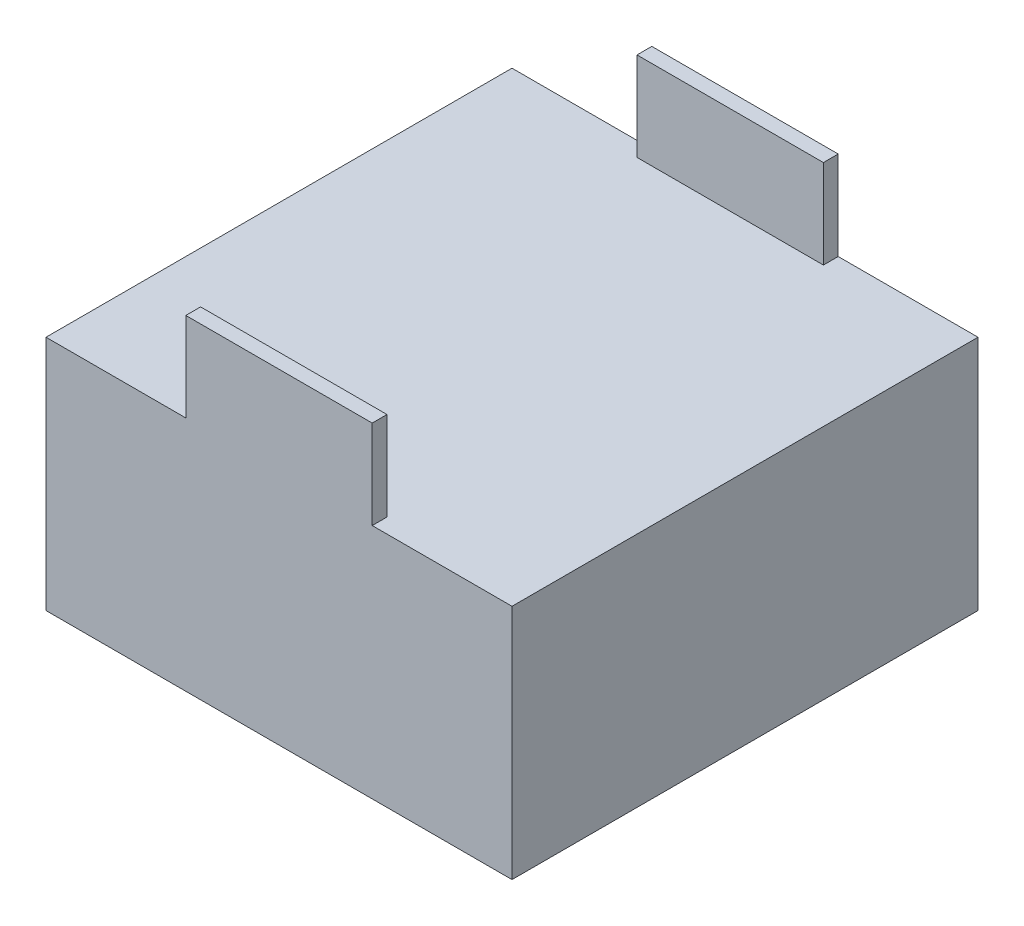
SolidWorks part; units mm, degrees
ref_plane "Front Plane" through (0, 0, 0) normal (0, 0, 1) x (1, 0, 0)
ref_plane "Top Plane" through (0, 0, 0) normal (0, 1, 0) x (1, 0, 0)
ref_plane "Right Plane" through (0, 0, 0) normal (1, 0, 0) x (0, 0, -1)
sketch "Sketch1" plane through (0, 0, 0) normal (0, 1, 0) x (1, 0, 0)
  line L1 (0, 0) -> (49.9999, 0)
  line L2 (0, 0) -> (0, 49.9999)
  line L3 (0, 49.9999) -> (49.9999, 49.9999)
  line L4 (49.9999, 0) -> (49.9999, 49.9999)
  dimension "D1" = 49.9999
extrude "Boss-Extrude1" add sketch "Sketch1" along normal blind 25.4
sketch "Sketch2" plane through (0, 25.4, 0) normal (0, 1, 0) x (1, 0, 0)
  line L0 (0, 0) -> (49.9999, 0) construction
  line L1 (14.9999, 0) -> (35, 0)
  line L2 (14.9999, 0) -> (14.9999, 1.5875)
  line L3 (14.9999, 1.5875) -> (35, 1.5875)
  line L4 (35, 0) -> (35, 1.5875)
  line L5 (24.9999, 49.9999) -> (25, 0) construction
  line L6 (49.9999, 49.9999) -> (0, 49.9999) construction
  line L7 (0, 25) -> (49.9999, 24.9999) construction
  line L8 (0, 49.9999) -> (0, 0) construction
  line L9 (49.9999, 0) -> (49.9999, 49.9999) construction
  line L10 (35, 49.9999) -> (35, 48.4124)
  line L11 (14.9999, 48.4124) -> (35, 48.4124)
  line L12 (14.9999, 49.9999) -> (14.9999, 48.4124)
  line L13 (14.9999, 49.9999) -> (35, 49.9999)
  point P10 (25, 1.5875)
  point P21 (25, 48.4124)
  dimension "D1" = 20
  dimension "D2" = 1.5875
extrude "Boss-Extrude2" add sketch "Sketch2" along normal blind 9.525
